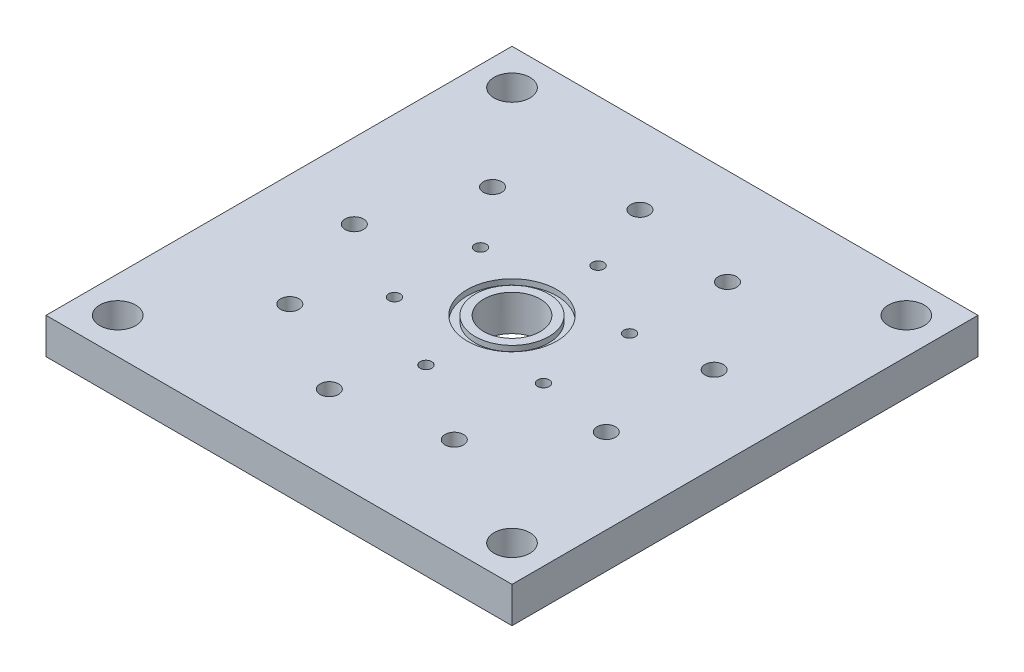
SolidWorks part; units mm, degrees
ref_plane "Front Plane" through (0, 0, 0) normal (0, 0, 1) x (1, 0, 0)
ref_plane "Top Plane" through (0, 0, 0) normal (0, 1, 0) x (1, 0, 0)
ref_plane "Right Plane" through (0, 0, 0) normal (1, 0, 0) x (0, 0, -1)
sketch "Sketch1" plane through (0, 0, 0) normal (0, 1, 0) x (1, 0, 0)
  line L1 (-41.275, -41.275) -> (41.275, -41.275)
  line L2 (-41.275, -41.275) -> (-41.275, 41.275)
  line L3 (-41.275, 41.275) -> (41.275, 41.275)
  line L4 (41.275, -41.275) -> (41.275, 41.275)
  line L5 (-41.275, -41.275) -> (41.275, 41.275) construction
  line L6 (-41.275, 41.275) -> (41.275, -41.275) construction
  point P0 (0, 0)
  dimension "D1" = 82.55
  dimension "D2" = 82.55
extrude "Boss-Extrude1" add sketch "Sketch1" along normal blind 6.35
sketch "Sketch2" plane through (0, 6.35, 0) normal (0, 1, 0) x (1, 0, 0)
  circle A0 centre (0, 0) radius 5
  dimension "D1" = 10
extrude "Cut-Extrude1" cut sketch "Sketch2" against normal up to next
sketch "Sketch4" plane through (0, 6.35, 0) normal (0, 1, 0) x (1, 0, 0)
  circle A0 centre (0, 0) radius 6.5278
  circle A1 centre (0, 0) radius 7.9248
  dimension "D1" = 1.397
extrude "Cut-Extrude3" cut sketch "Sketch4" against normal blind 0.9779
sketch "Sketch5" plane through (0, 6.35, 0) normal (0, 1, 0) x (1, 0, 0)
  circle A0 centre (0, 0) radius 15.24 construction
  circle A1 centre (0, -15.24) radius 1.0325
  dimension "D1" = 2.065
extrude "Cut-Extrude4" cut sketch "Sketch5" against normal blind 3.175
pattern_circular "CirPattern1" count 6 over 360 about axis through (0, 0, 0) along (0, 1, 0) of "Cut-Extrude4"
sketch "Sketch6" plane through (0, 6.35, 0) normal (0, 1, 0) x (1, 0, 0)
  line L0 (0, 0) -> (13.97, -24.1967) construction
  circle A0 centre (0, 0) radius 27.94 construction
  circle A1 centre (13.97, -24.1967) radius 1.632
extrude "Cut-Extrude5" cut sketch "Sketch6" against normal up to next (6.35 mm away)
pattern_circular "CirPattern2" count 9 over 360 about axis through (0, 0, 0) along (0, 1, 0) of "Cut-Extrude5"
sketch "Sketch7" plane through (0, 6.35, 0) normal (0, 1, 0) x (1, 0, 0)
  line L0 (41.275, 41.275) -> (-41.275, 41.275) construction
  line L1 (41.275, -41.275) -> (41.275, 41.275) construction
  line L2 (0, 0) -> (41.275, 0) construction
  line L3 (0, 0) -> (0, 41.275) construction
  circle A0 centre (34.925, 34.925) radius 3.175
  circle A1 centre (0, 0) radius 38.1 construction
  circle A2 centre (34.925, -34.925) radius 3.175
  circle A3 centre (-34.925, -34.925) radius 3.175
  circle A4 centre (-34.925, 34.925) radius 3.175
  circle A5 centre (34.925, 34.925) radius 5.5562 construction
  dimension "D1" = 6.35
  dimension "D2" = 6.35
extrude "Cut-Extrude6" cut sketch "Sketch7" against normal up to next
equation "\"AnnulusPlateThickness\"= 0.25"
equation "\"D1@Boss-Extrude1\"=\"AnnulusPlateThickness\""
equation "\"CenterRadius\"= 0.19685"
equation "\"D1@Sketch2\"=\"CenterRadius\"*2"
